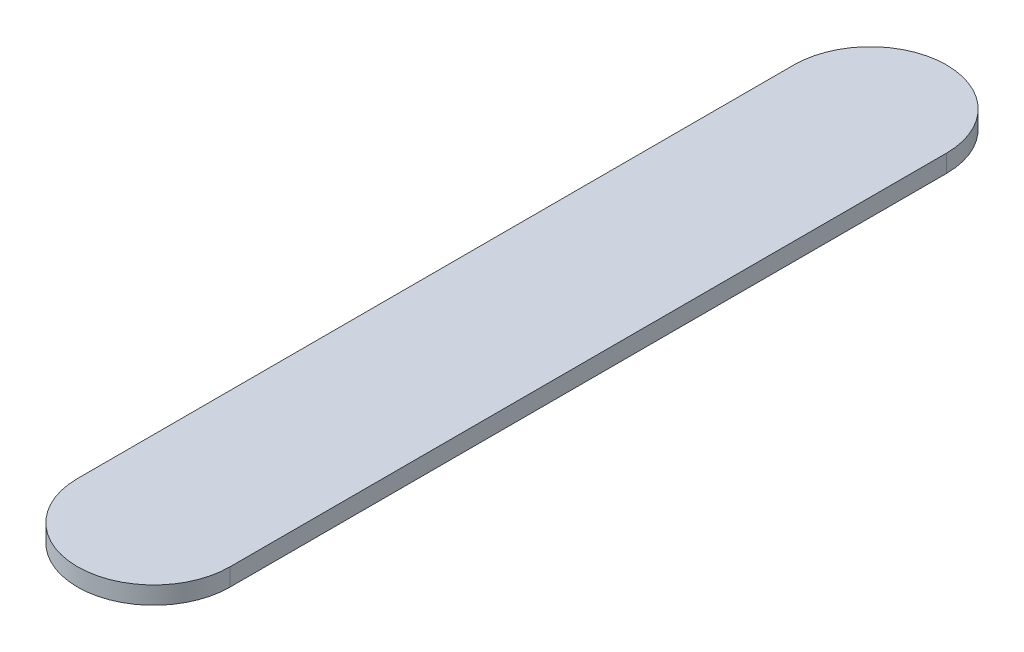
SolidWorks part; units mm, degrees
ref_plane "前视基准面" through (0, 0, 0) normal (0, 0, 1) x (1, 0, 0)
ref_plane "上视基准面" through (0, 0, 0) normal (0, 1, 0) x (1, 0, 0)
ref_plane "右视基准面" through (0, 0, 0) normal (1, 0, 0) x (0, 0, -1)
sketch "草图1" plane through (0, 0, 0) normal (0, 1, 0) x (1, 0, 0)
  line L0 (0, 0) -> (0, 30.5) construction
  line L2 (-6.5, 30.5) -> (-6.5, -30.5)
  line L4 (6.5, 30.5) -> (6.5, -30.5)
  line L5 (0, 0) -> (-16.8084, 0) construction
  arc A0 (6.5, 30.5) -> (-6.5, 30.5) centre (0, 30.5) ccw
  arc A1 (-6.5, -30.5) -> (6.5, -30.5) centre (0, -30.5) ccw
  point P0 (0, 0)
  point P3 (0, -37)
  point P7 (0, 37)
  dimension "D2" = 74
  dimension "D1" = 13
extrude "凸台-拉伸1" add sketch "草图1" along normal blind 1.5
